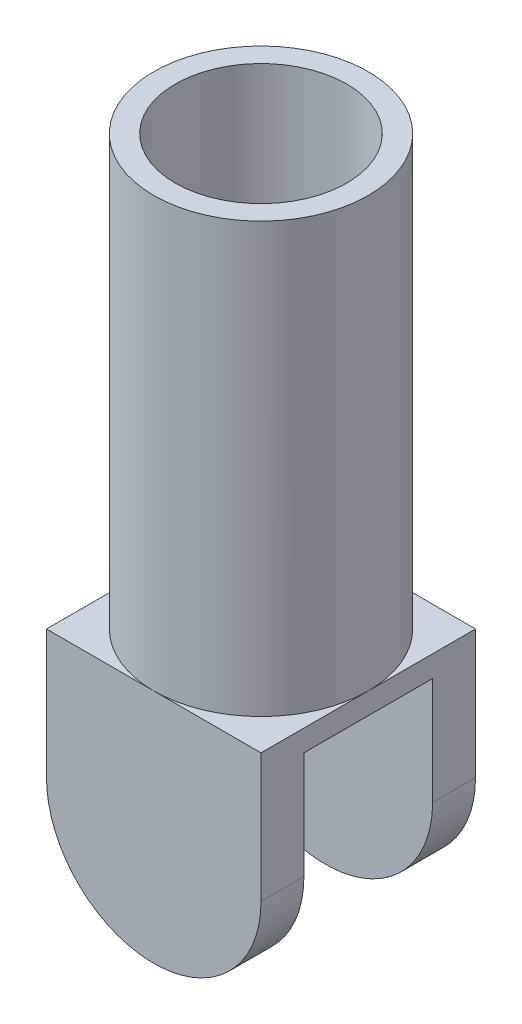
SolidWorks part; units mm, degrees
ref_plane "Front" through (0, 0, 0) normal (0, 0, 1) x (1, 0, 0)
ref_plane "Top" through (0, 0, 0) normal (0, 1, 0) x (1, 0, 0)
ref_plane "Right" through (0, 0, 0) normal (1, 0, 0) x (0, 0, -1)
sketch "草图1" plane through (0, 0, 0) normal (0, 1, 0) x (1, 0, 0)
  line L1 (-5, 5) -> (5, 5)
  line L2 (-5, 5) -> (-5, -5)
  line L3 (-5, -5) -> (5, -5)
  line L4 (5, 5) -> (5, -5)
  dimension "D1" = 10
  dimension "D2" = 10
  dimension "D3" = 5
  dimension "D4" = 5
extrude "凸台-拉伸1" add sketch "草图1" along normal blind 11
sketch "草图2" plane through (0, 11, 0) normal (0, 1, 0) x (1, 0, 0)
  circle A0 centre (0, 0) radius 5
  circle A1 centre (0, 0) radius 4
extrude "凸台-拉伸2" add sketch "草图2" along normal blind 20
sketch "草图3" plane through (5, 0, 0) normal (1, 0, 0) x (0, 0, -1)
  line L0 (-5, 0) -> (5, 0) construction
  line L1 (-3, 0) -> (3, 0)
  line L2 (-3, 0) -> (-3, 10)
  line L3 (-3, 10) -> (3, 10)
  line L4 (3, 0) -> (3, 10)
  dimension "D1" = 10
  dimension "D2" = 3
  dimension "D3" = 6
extrude "切除-拉伸1" cut sketch "草图3" against normal blind 60
sketch "草图4" plane through (0, 0, 5) normal (0, 0, 1) x (1, 0, 0)
  line L2 (-5, 5) -> (-5, -1.7608)
  line L3 (-5, -1.7608) -> (5, -1.7608)
  line L4 (5, 5) -> (5, -1.7608)
  arc A0 (-5, 5) -> (5, 5) centre (0, 5) ccw
extrude "切除-拉伸2" cut sketch "草图4" against normal blind 60
